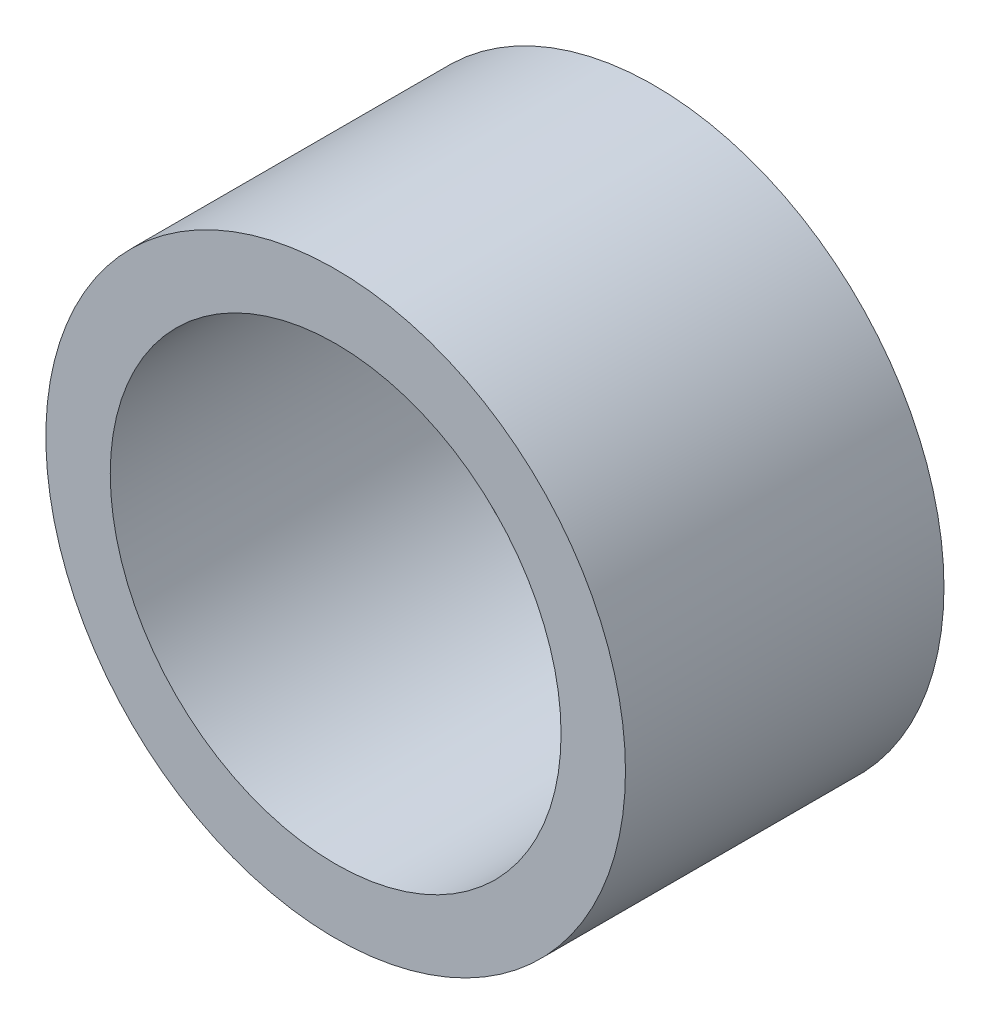
SolidWorks part; units mm, degrees
ref_plane "Front Plane" through (0, 0, 0) normal (0, 0, 1) x (1, 0, 0)
ref_plane "Top Plane" through (0, 0, 0) normal (0, 1, 0) x (1, 0, 0)
ref_plane "Right Plane" through (0, 0, 0) normal (1, 0, 0) x (0, 0, -1)
sketch "Sketch1" plane through (0, 0, 0) normal (0, 0, 1) x (1, 0, 0)
  circle A0 centre (0, 0) radius 11.1125
  circle A1 centre (0, 0) radius 14.2875
  dimension "D1" = 22.225
  dimension "D2" = 3.175
extrude "Boss-Extrude1" add sketch "Sketch1" along normal blind 15.7023
